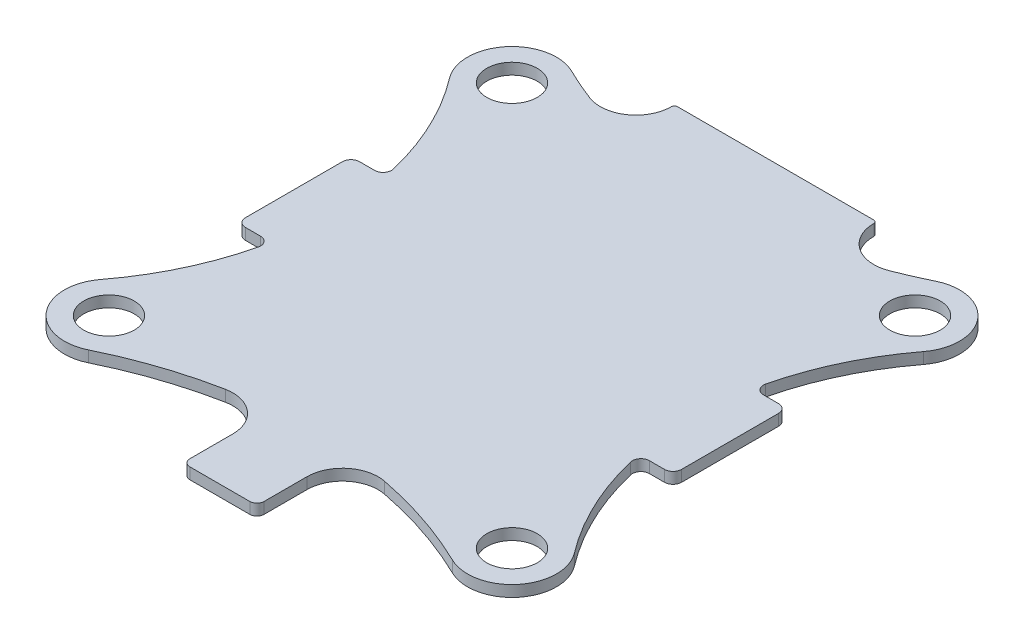
SolidWorks part; units mm, degrees
ref_plane "Front Plane" through (0, 0, 0) normal (0, 0, 1) x (1, 0, 0)
ref_plane "Top Plane" through (0, 0, 0) normal (0, 1, 0) x (1, 0, 0)
ref_plane "Right Plane" through (0, 0, 0) normal (1, 0, 0) x (0, 0, -1)
sketch "Sketch1" plane through (0, 0, 0) normal (0, 1, 0) x (1, 0, 0)
  line L0 (-17.9605, 17.9605) -> (17.9605, -17.9605) construction
  line L1 (-15.875, -17.78) -> (15.875, -17.78) construction
  line L2 (-15.875, -17.78) -> (-15.875, 17.78) construction
  line L3 (-15.875, 17.78) -> (15.875, 17.78) construction
  line L4 (15.875, -17.78) -> (15.875, 17.78) construction
  line L5 (-17.9605, -17.9605) -> (17.9605, 17.9605) construction
  line L6 (-20.7668, -15.1542) -> (-15.1542, -20.7668) construction
  line L7 (0, -17.78) -> (0, 17.78) construction
  line L8 (-15.875, 0) -> (15.875, 0) construction
  line L9 (20.7668, -15.1542) -> (15.1542, -20.7668) construction
  line L10 (-20.7668, 15.1542) -> (-15.1542, 20.7668) construction
  line L11 (20.7668, 15.1542) -> (15.1542, 20.7668) construction
  line L12 (-17.331, -5.08) -> (-18.669, -5.08)
  line L13 (-19.431, -4.318) -> (-19.431, 4.318)
  line L14 (-18.669, 5.08) -> (-17.331, 5.08)
  line L15 (18.669, 5.08) -> (17.331, 5.08)
  line L16 (19.431, -4.318) -> (19.431, 4.318)
  line L17 (-3.302, -21.5813) -> (-3.302, -25.4)
  line L18 (-2.667, -26.035) -> (2.667, -26.035)
  line L19 (3.302, -25.4) -> (3.302, -21.5813)
  line L20 (-9.017, 23.2303) -> (-9.017, 23.241)
  line L21 (-8.763, 23.495) -> (8.763, 23.495)
  line L22 (9.017, 23.241) -> (9.017, 23.2303)
  line L28 (17.331, -5.08) -> (18.669, -5.08)
  circle A0 centre (-17.9605, -17.9605) radius 3.9688 construction
  circle A1 centre (17.9605, -17.9605) radius 3.9688 construction
  circle A2 centre (17.9605, 17.9605) radius 3.9688 construction
  circle A3 centre (-17.9605, 17.9605) radius 3.9688 construction
  arc A4 (-21.1194, 15.5579) -> (-21.1194, -15.5579) centre (-41.5741, 0) cw construction
  arc A5 (-16.2197, 21.5271) -> (16.2197, 21.5271) centre (0, 54.7579) ccw construction
  arc A6 (-16.2197, -21.5271) -> (16.2197, -21.5271) centre (0, -54.7579) cw construction
  arc A7 (21.1194, 15.5579) -> (21.1194, -15.5579) centre (41.5741, 0) ccw construction
  arc A8 (-21.1194, 15.5579) -> (-16.2197, 21.5271) centre (-17.9605, 17.9605) cw
  arc A9 (16.2197, 21.5271) -> (21.1194, 15.5579) centre (17.9605, 17.9605) cw
  arc A10 (21.1194, -15.5579) -> (16.2197, -21.5271) centre (17.9605, -17.9605) cw
  arc A11 (-21.1194, -15.5579) -> (-16.2197, -21.5271) centre (-17.9605, -17.9605) ccw
  circle A12 centre (-17.9605, -17.9605) radius 2.25
  circle A13 centre (17.9605, -17.9605) radius 2.25
  circle A14 centre (17.9605, 17.9605) radius 2.25
  circle A15 centre (-17.9605, 17.9605) radius 2.25
  arc A16 (-21.1194, -15.5579) -> (-16.5902, -6.0205) centre (-41.5741, 0) ccw
  arc A17 (-17.331, -5.08) -> (-16.5902, -6.0205) centre (-17.331, -5.842) cw
  arc A18 (-21.1194, 15.5579) -> (-16.5902, 6.0205) centre (-41.5741, 0) cw
  arc A19 (-16.5902, 6.0205) -> (-17.331, 5.08) centre (-17.331, 5.842) cw
  arc A20 (-18.669, 5.08) -> (-19.431, 4.318) centre (-18.669, 4.318) ccw
  arc A21 (-19.431, -4.318) -> (-18.669, -5.08) centre (-18.669, -4.318) ccw
  arc A22 (16.5902, 6.0205) -> (17.331, 5.08) centre (17.331, 5.842) ccw
  arc A23 (21.1194, 15.5579) -> (16.5902, 6.0205) centre (41.5741, 0) ccw
  arc A24 (21.1194, -15.5579) -> (16.5902, -6.0205) centre (41.5741, 0) cw
  arc A25 (17.331, -5.08) -> (16.5902, -6.0205) centre (17.331, -5.842) ccw
  arc A26 (19.431, -4.318) -> (18.669, -5.08) centre (18.669, -4.318) cw
  arc A27 (18.669, 5.08) -> (19.431, 4.318) centre (18.669, 4.318) cw
  arc A28 (-16.2197, -21.5271) -> (-7.0854, -18.4652) centre (0, -54.7579) cw
  arc A29 (16.2197, -21.5271) -> (7.0854, -18.4652) centre (0, -54.7579) ccw
  arc A30 (-7.0854, -18.4652) -> (-3.302, -21.5813) centre (-6.477, -21.5813) cw
  arc A31 (7.0854, -18.4652) -> (3.302, -21.5813) centre (6.477, -21.5813) ccw
  arc A32 (-3.302, -25.4) -> (-2.667, -26.035) centre (-2.667, -25.4) ccw
  arc A33 (3.302, -25.4) -> (2.667, -26.035) centre (2.667, -25.4) cw
  arc A34 (-16.2197, 21.5271) -> (-13.3372, 20.269) centre (0, 54.7579) ccw
  arc A35 (16.2197, 21.5271) -> (13.3372, 20.269) centre (0, 54.7579) cw
  arc A36 (-9.017, 23.2303) -> (-13.3372, 20.269) centre (-12.192, 23.2303) cw
  arc A37 (9.017, 23.2303) -> (13.3372, 20.269) centre (12.192, 23.2303) ccw
  arc A38 (-8.763, 23.495) -> (-9.017, 23.241) centre (-8.763, 23.241) ccw
  arc A39 (8.763, 23.495) -> (9.017, 23.241) centre (8.763, 23.241) cw
  point P4 (0, 17.78)
  point P6 (15.875, 0)
  point P11 (0, 0)
  point P12 (0, 0)
  point P19 (-17.9605, -17.9605)
  point P60 (-19.431, 5.08)
  point P63 (-19.431, -5.08)
  point P72 (19.431, -5.08)
  point P73 (19.431, 5.08)
  point P82 (3.302, -17.9277)
  point P85 (-3.302, -26.035)
  point P88 (3.302, -26.035)
  point P95 (-9.017, 18.8962)
  point P98 (9.017, 18.8962)
  point P102 (-9.017, 23.495)
  point P105 (9.017, 23.495)
  dimension "D3" = 7.9375
  dimension "D8" = 0.762
  dimension "D9" = 0.762
  dimension "D10" = 0.762
  dimension "D11" = 0.762
  dimension "D14" = 3.175
  dimension "D15" = 3.175
  dimension "D16" = 0.635
  dimension "D17" = 0.635
  dimension "D20" = 3.175
  dimension "D21" = 3.175
  dimension "D22" = 4.5
  dimension "D23" = 0.254
  dimension "D24" = 0.254
  dimension "D1" = 31.75
  dimension "D2" = 35.56
  dimension "D4" = 50.8
  dimension "D5" = 3.556
  dimension "D6" = 5.08
  dimension "D7" = 5.08
  dimension "D12" = 6.604
  dimension "D13" = 8.255
  dimension "D18" = 5.715
  dimension "D19" = 18.034
extrude "Boss-Extrude2" add sketch "Sketch1" along normal blind 1 contours A12 | A13 | A14 | A15 | A28 A30 L17 A32 L18 A33 L19 A31 A29 A10 A24 A25 L28 A26 L16 A27 L15 A22 A23 A9 A35 A37 L22 A39 L21 A38 L20 A36 A34 A8 A18 A19 L14 A20 L13 A21 L12 A17 A16 A11
